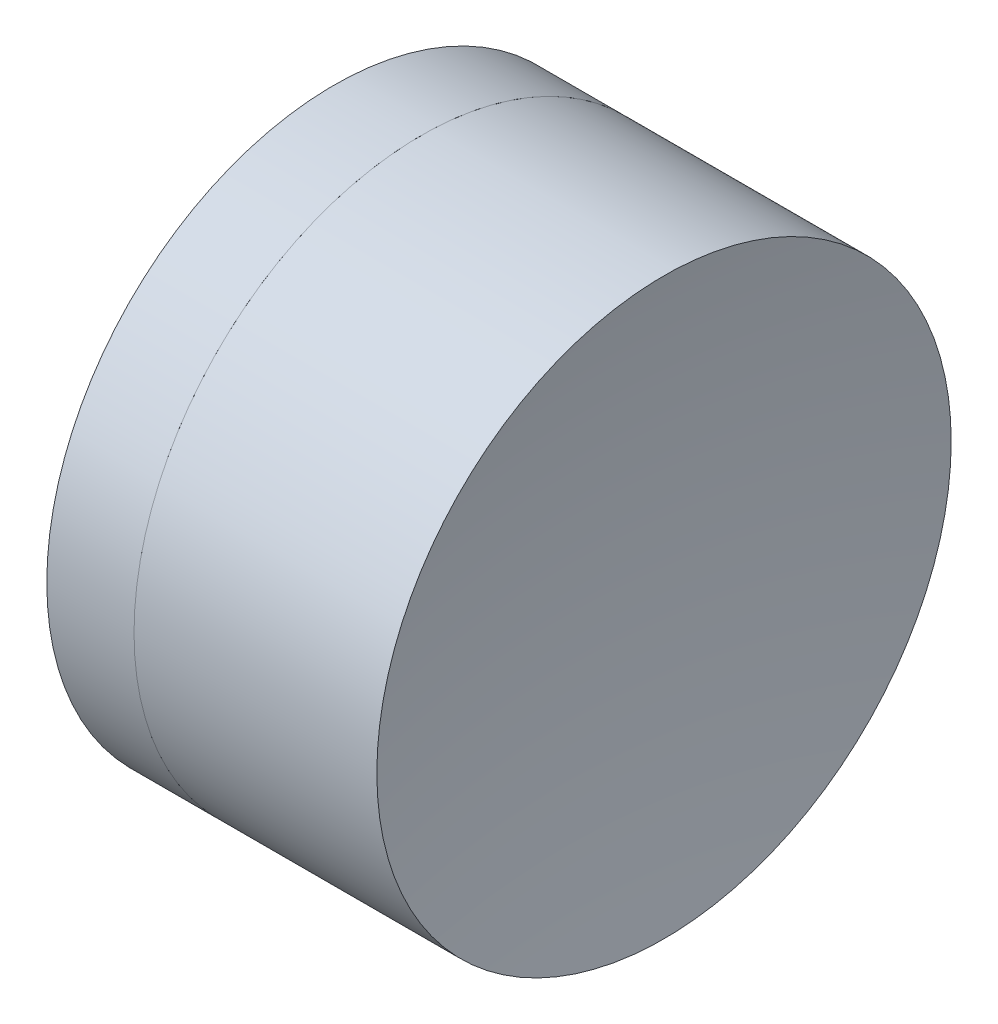
SolidWorks part; units mm, degrees
ref_plane "前视基准面" through (0, 0, 0) normal (0, 0, 1) x (1, 0, 0)
ref_plane "上视基准面" through (0, 0, 0) normal (0, 1, 0) x (1, 0, 0)
ref_plane "右视基准面" through (0, 0, 0) normal (1, 0, 0) x (0, 0, -1)
sketch "草图1" plane through (0, 0, 0) normal (0, 1, 0) x (1, 0, 0)
  line L0 (-0.8161, 0) -> (4.9474, 0) construction
  line L1 (2.5695, -2.5) -> (3.3288, -2.5)
  line L2 (2.5695, 2.5) -> (3.3288, 2.5)
  arc A0 (3.3288, -2.5) -> (3.3288, 2.5) centre (-1.514, 0) ccw
  arc A1 (2.5695, 2.5) -> (2.5695, -2.5) centre (7.186, 0) ccw
  point P4 (4.9474, 0)
  point P10 (1.936, 0)
  point P11 (3.936, 0)
  dimension "D3" = 5.25
  dimension "D4" = 5.45
  dimension "D1" = 2.5
  dimension "D2" = 2.5
  dimension "D5" = 2
revolve "旋转1" add sketch "草图1" angle 360 about L0
sketch "草图2" plane through (0, 0, 0) normal (0, 1, 0) x (1, 0, 0)
  line L0 (-0.5519, 0) -> (10.2522, 0) construction
  line L2 (3.3288, 2.5) -> (5.4425, 2.5)
  line L3 (3.3288, -2.5) -> (5.4425, -2.5)
  arc A0 (5.4425, 2.5) -> (5.4425, -2.5) centre (20.476, 0) ccw
  arc A1 (3.3288, -2.5) -> (3.3288, 2.5) centre (-1.514, 0) ccw construction
  arc A2 (3.3288, -2.5) -> (3.3288, 2.5) centre (-1.514, 0) ccw
  point P4 (3.936, 0)
  point P10 (5.236, 0)
  dimension "D1" = 15.24
  dimension "D2" = 1.3
revolve "旋转2" add sketch "草图2" angle 360 about L0
